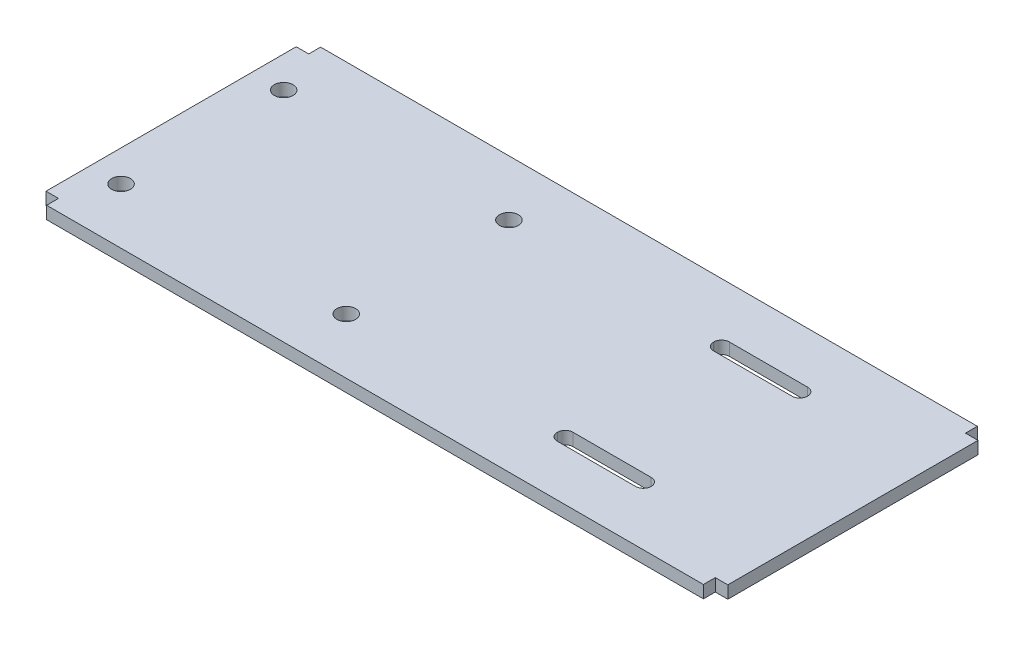
SolidWorks part; units mm, degrees
ref_plane "Front Plane" through (0, 0, 0) normal (0, 0, 1) x (1, 0, 0)
ref_plane "Top Plane" through (0, 0, 0) normal (0, 1, 0) x (1, 0, 0)
ref_plane "Right Plane" through (0, 0, 0) normal (1, 0, 0) x (0, 0, -1)
sketch "Sketch1" plane through (0, 0, 0) normal (0, 1, 0) x (1, 0, 0)
  line L0 (-66.675, 25.4) -> (-69.215, 25.4)
  line L1 (-66.675, -27.813) -> (66.675, -27.813)
  line L2 (-66.675, 25.4) -> (-66.675, 27.813)
  line L3 (-66.675, 27.813) -> (66.675, 27.813)
  line L4 (66.675, 25.4) -> (66.675, 27.813)
  line L5 (-66.675, -27.813) -> (66.675, 27.813) construction
  line L6 (-66.675, 27.813) -> (66.675, -27.813) construction
  line L7 (-69.215, 25.4) -> (-69.215, -25.4)
  line L8 (-69.215, 0) -> (-66.675, 0) construction
  line L9 (0, 0) -> (0, 27.813) construction
  line L10 (-66.675, -25.4) -> (-69.215, -25.4)
  line L11 (66.675, -25.4) -> (69.215, -25.4)
  line L12 (66.675, 25.4) -> (69.215, 25.4)
  line L13 (69.215, 25.4) -> (69.215, -25.4)
  line L14 (-66.675, -27.813) -> (-66.675, -25.4)
  line L15 (66.675, -25.4) -> (66.675, -27.813)
  point P0 (0, 0)
  dimension "D1" = 133.35
  dimension "D2" = 55.626
  dimension "D3" = 2.54
  dimension "D4" = 25.4
extrude "Boss-Extrude1" add sketch "Sketch1" along normal blind 2.54
sketch "Sketch2" plane through (0, 2.54, 0) normal (0, 1, 0) x (1, 0, 0)
  line L0 (-66.675, -27.813) -> (66.675, -27.813) construction
  line L1 (-62.865, -16.51) -> (-17.145, -16.51)
  line L2 (-62.865, -16.51) -> (-62.865, 16.51)
  line L3 (-62.865, 16.51) -> (-17.145, 16.51)
  line L4 (-17.145, -16.51) -> (-17.145, 16.51)
  line L5 (-62.865, -16.51) -> (-17.145, 16.51) construction
  line L6 (-62.865, 16.51) -> (-17.145, -16.51) construction
  line L7 (-69.215, 25.4) -> (-69.215, -25.4) construction
  circle A0 centre (-62.865, 16.51) radius 1.905
  circle A1 centre (-17.145, 16.51) radius 1.905
  circle A2 centre (-17.145, -16.51) radius 1.905
  circle A3 centre (-62.865, -16.51) radius 1.905
  point P0 (-40.005, 0)
  point P7 (0, -27.813)
  dimension "D5" = 3.81
  dimension "D6" = 3.81
  dimension "D7" = 3.81
  dimension "D8" = 3.81
  dimension "D1" = 33.02
  dimension "D2" = 45.72
  dimension "D3" = 11.303
  dimension "D4" = 6.35
extrude "Cut-Extrude1" cut sketch "Sketch2" against normal through all contours L3 A0 L2 | L4 A1 L3 | L2 A0 L3 | L3 A1 L4 | L4 A2 L1 | L1 A2 L4 | L2 A3 L1 | L1 A3 L2
sketch "Sketch3" plane through (0, 2.54, 0) normal (0, 1, 0) x (1, 0, 0)
  line L0 (0, 0) -> (69.215, 0) construction
  line L1 (69.215, 25.4) -> (69.215, -25.4) construction
  line L2 (34.6075, 0) -> (34.6075, -15.875) construction
  line L3 (44.1325, 15.8877) -> (44.1325, 15.8623)
  line L4 (42.5577, -17.4625) -> (26.6573, -17.4625)
  line L5 (44.1325, -15.8877) -> (44.1325, -15.8623)
  line L6 (42.5577, -14.2875) -> (26.6573, -14.2875)
  line L7 (25.0825, -15.8877) -> (25.0825, -15.8623)
  line L8 (44.1325, -17.4625) -> (25.0825, -14.2875) construction
  line L9 (44.1325, -14.2875) -> (25.0825, -17.4625) construction
  line L10 (42.5577, 17.4625) -> (26.6573, 17.4625)
  line L11 (25.0825, 15.8877) -> (25.0825, 15.8623)
  line L12 (42.5577, 14.2875) -> (26.6573, 14.2875)
  arc A0 (26.6573, -17.4625) -> (25.0825, -15.8877) centre (26.6573, -15.8877) cw
  arc A1 (44.1325, -15.8877) -> (42.5577, -17.4625) centre (42.5577, -15.8877) cw
  arc A2 (44.1325, -15.8623) -> (42.5577, -14.2875) centre (42.5577, -15.8623) ccw
  arc A3 (26.6573, -14.2875) -> (25.0825, -15.8623) centre (26.6573, -15.8623) ccw
  arc A4 (25.0825, 15.8623) -> (26.6573, 14.2875) centre (26.6573, 15.8623) ccw
  arc A5 (42.5577, 14.2875) -> (44.1325, 15.8623) centre (42.5577, 15.8623) ccw
  arc A6 (44.1325, 15.8877) -> (42.5577, 17.4625) centre (42.5577, 15.8877) ccw
  arc A7 (26.6573, 17.4625) -> (25.0825, 15.8877) centre (26.6573, 15.8877) ccw
  point P29 (25.0825, 14.2875)
  point P32 (44.1325, 14.2875)
  point P35 (44.1325, 17.4625)
  point P38 (25.0825, 17.4625)
  dimension "D4" = 1.5748
  dimension "D5" = 1.5748
  dimension "D1" = 19.05
  dimension "D2" = 15.875
  dimension "D3" = 3.175
extrude "Cut-Extrude2" cut sketch "Sketch3" against normal through all
